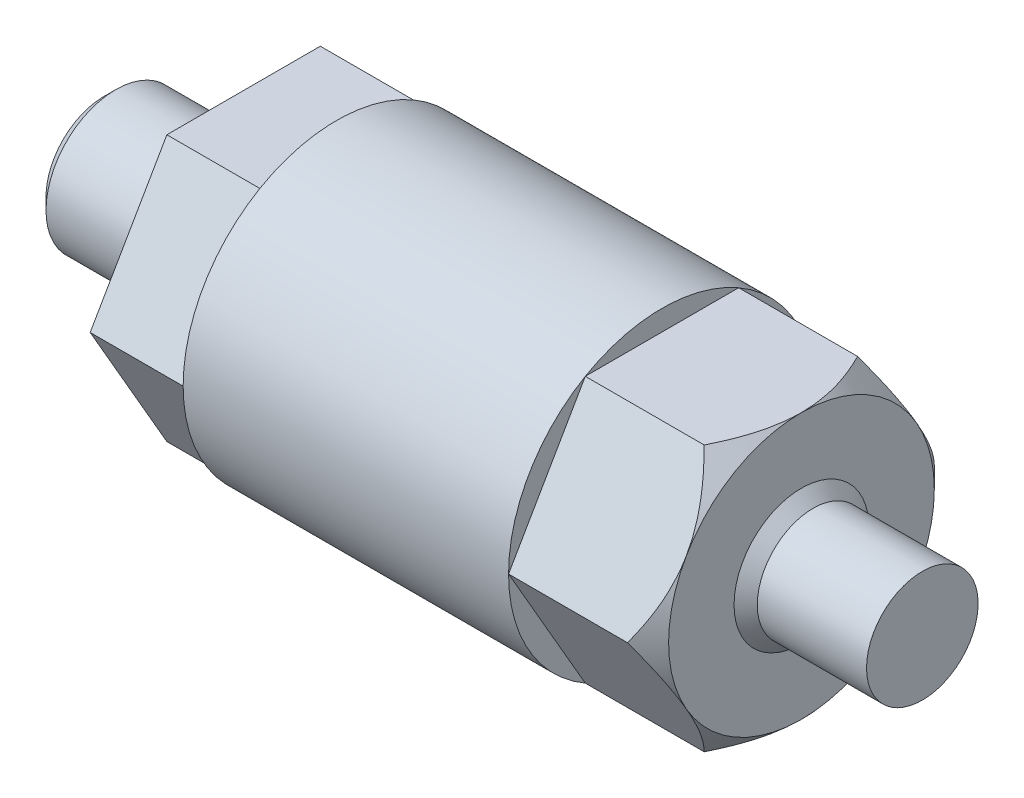
SolidWorks part; units mm, degrees
material "1.6523 (20NiCrMoS2-2)"
ref_plane "Front Plane" through (0, 0, 0) normal (0, 0, 1) x (1, 0, 0)
ref_plane "Top Plane" through (0, 0, 0) normal (0, 1, 0) x (1, 0, 0)
ref_plane "Right Plane" through (0, 0, 0) normal (1, 0, 0) x (0, 0, -1)
sketch "Sketch1" plane through (0, 0, 0) normal (0, 1, 0) x (1, 0, 0)
  line L0 (0, 6.6) -> (0, 3)
  line L1 (0, 3) -> (-6, 3)
  line L2 (-6, 3) -> (-6, 0)
  line L4 (29.2, 0) -> (29.2, 2.4)
  line L5 (29.2, 2.4) -> (24, 2.4)
  line L6 (24, 2.4) -> (24, 6.6)
  line L7 (24, 6.6) -> (0, 6.6)
  line L8 (-26.1864, 0) -> (39.5763, 0) construction
  line L9 (-6, 0) -> (29.2, 0)
  dimension "D1" = 6
  dimension "D2" = 6
  dimension "D3" = 24
  dimension "D4" = 5.2
  dimension "D5" = 13.2
  dimension "D6" = 4.8
revolve "Revolve1" add sketch "Sketch1" angle 360 about L8
sketch "Sketch2" plane through (24, 0, 0) normal (1, 0, 0) x (0, 0, -1)
  line L1 (3.3, -5.7158) -> (6.6, 0)
  line L2 (6.6, 0) -> (3.3, 5.7158)
  line L3 (3.3, 5.7158) -> (-3.3, 5.7158)
  line L4 (-3.3, 5.7158) -> (-6.6, 0)
  line L5 (-6.6, 0) -> (-3.3, -5.7158)
  line L6 (-3.3, -5.7158) -> (3.3, -5.7158)
  circle A0 centre (0, 0) radius 5.7158 construction
  circle A1 centre (0, 0) radius 6.6 construction
extrude "Cut-Extrude1" cut sketch "Sketch2" against normal blind 6 flip side to cut
sketch "Sketch3" plane through (0, 0, 0) normal (-1, 0, 0) x (0, 0, 1)
  line L1 (3.3, -5.7158) -> (6.6, 0)
  line L2 (6.6, 0) -> (3.3, 5.7158)
  line L3 (3.3, 5.7158) -> (-3.3, 5.7158)
  line L4 (-3.3, 5.7158) -> (-6.6, 0)
  line L5 (-6.6, 0) -> (-3.3, -5.7158)
  line L6 (-3.3, -5.7158) -> (3.3, -5.7158)
  circle A0 centre (0, 0) radius 5.7158 construction
  circle A1 centre (0, 0) radius 6.6 construction
extrude "Cut-Extrude2" cut sketch "Sketch3" against normal blind 4 flip side to cut
sketch "Sketch4" plane through (0, 0, 0) normal (0, 0, 1) x (1, 0, 0)
  line L0 (22.0196, 7.6961) -> (25.9804, 3.7354)
  line L1 (25.9804, 3.7354) -> (25.9804, 7.6961)
  line L2 (25.9804, 7.6961) -> (22.0196, 7.6961)
revolve "Cut-Revolve1" cut sketch "Sketch4" angle 360 about L8
chamfer "Chamfer1" distance 0.5 angle 45 2 edges at (24, 0, 2.4) (-6, 0, 3)
